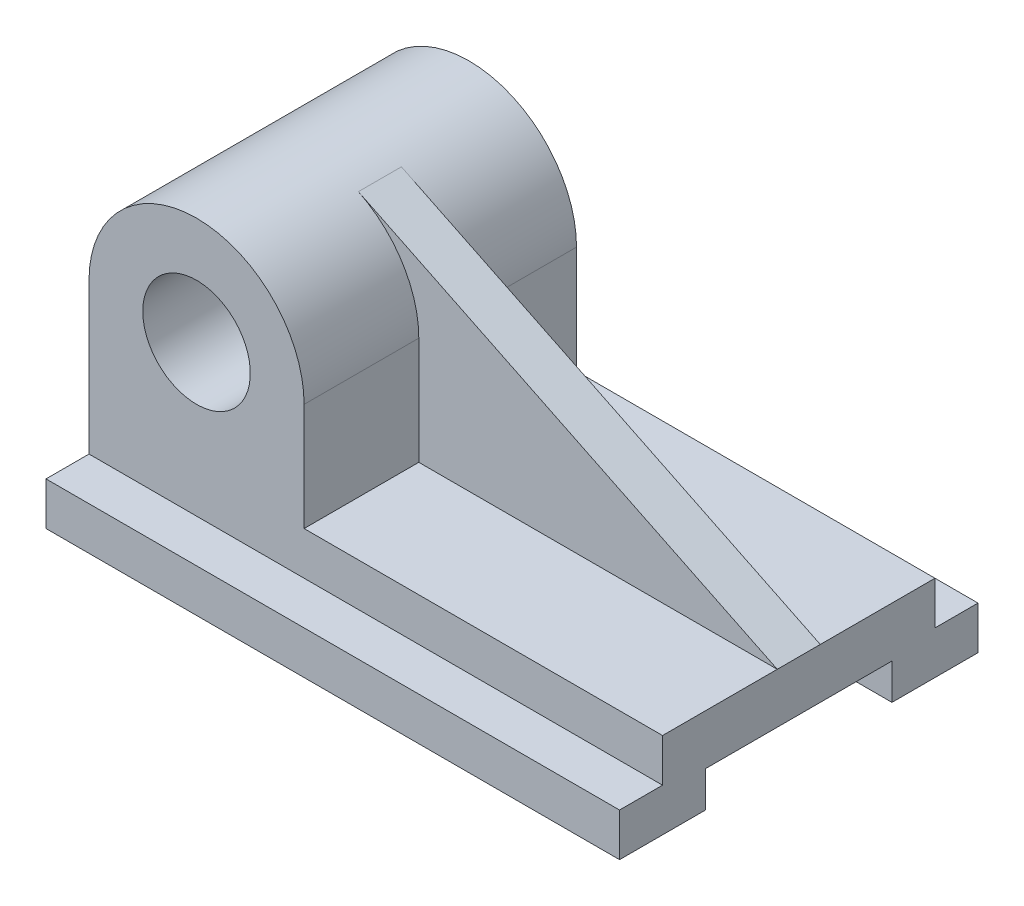
SolidWorks part; units mm, degrees
ref_plane "Front Plane" through (0, 0, 0) normal (0, 0, 1) x (1, 0, 0)
ref_plane "Top Plane" through (0, 0, 0) normal (0, 1, 0) x (1, 0, 0)
ref_plane "Right Plane" through (0, 0, 0) normal (1, 0, 0) x (0, 0, -1)
sketch "Sketch1" plane through (0, 0, 0) normal (1, 0, 0) x (0, 0, -1)
  line L0 (-26, -5) -> (-50, -5)
  line L1 (-26, 5) -> (26, 5)
  line L2 (-26, 5) -> (-26, -5)
  line L5 (-26, 5) -> (26, -5) construction
  line L6 (-26, -5) -> (26, 5) construction
  line L7 (-50, -5) -> (-50, 7)
  line L8 (-50, 7) -> (-38, 7)
  line L9 (-38, 7) -> (-38, 19)
  line L10 (38, 19) -> (38, 7)
  line L11 (-38, 19) -> (38, 19)
  line L12 (38, 7) -> (50, 7)
  line L13 (50, 7) -> (50, -5)
  line L14 (50, -5) -> (26, -5)
  line L15 (38, 19) -> (38, 7)
  line L16 (26, 5) -> (26, -5)
  point P0 (0, 0)
  point P6 (-38, -5)
  dimension "D1" = 52
  dimension "D2" = 12
  dimension "D3" = 24
  dimension "D4" = 12
  dimension "D5" = 24
  dimension "D6" = 24
  dimension "D7" = 12
  dimension "D8" = 10
  dimension "D9" = 100
extrude "Boss-Extrude1" add sketch "Sketch1" against normal blind 160 contours L1 L16 L14 L13 L12 L10 L11 L9 L8 L7 L0 L2
sketch "Sketch2" plane through (0, 0, -38) normal (0, 0, -1) x (-1, 0, 0)
  line L0 (160, 19) -> (160, 49)
  line L1 (160, 19) -> (100, 19)
  line L2 (160, 19) -> (0, 19) construction
  line L3 (100, 19) -> (100, 49)
  line L4 (100, 49) -> (160, 49) construction
  circle A0 centre (130, 49) radius 15
  arc A1 (160, 49) -> (100, 49) centre (130, 49) ccw
  dimension "D4" = 30
  dimension "D5" = 60
  dimension "D1" = 30
  dimension "D3" = 60
extrude "Boss-Extrude4" add sketch "Sketch2" against normal blind 76 contours L0 A1 L3 L1 | A0
sketch "Sketch5" plane through (0, 0, 0) normal (0, 0, 1) x (1, 0, 0)
  line L0 (0, 19) -> (-116.8539, 75.9663)
  arc A0 (-100, 49) -> (-160, 49) centre (-130, 49) ccw construction
  arc A1 (-100, 49) -> (-160, 49) centre (-130, 49) ccw construction
rib "Rib4" sketch "Sketch5" sketch "Sketch5" thickness 12 extrusion direction parallel to sketch draft on no parameters "D1"=12
